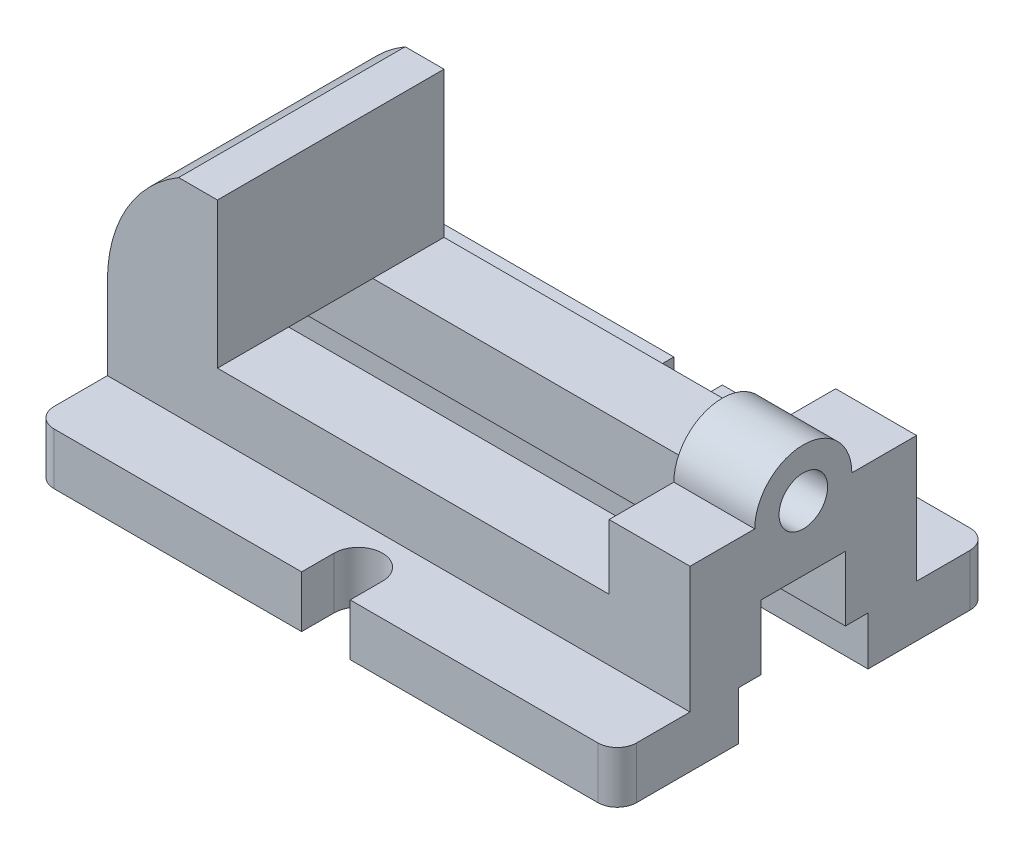
SolidWorks part; units mm, degrees
material "Malleable Cast Iron"
ref_plane "Front Plane" through (0, 0, 0) normal (0, 0, 1) x (1, 0, 0)
ref_plane "Top Plane" through (0, 0, 0) normal (0, 1, 0) x (1, 0, 0)
ref_plane "Right Plane" through (0, 0, 0) normal (1, 0, 0) x (0, 0, -1)
sketch "Sketch1" plane through (0, 0, 0) normal (1, 0, 0) x (0, 0, -1)
  line L0 (0, -17.5) -> (0, 17.5) construction
  line L1 (13, 17.5) -> (35, 17.5)
  line L2 (35, 17.5) -> (35, -1.5)
  line L3 (35, -1.5) -> (57.5, -1.5)
  line L4 (57.5, -1.5) -> (57.5, -17.5)
  line L5 (57.5, -17.5) -> (20, -17.5)
  line L6 (20, -17.5) -> (20, -2.5)
  line L7 (20, -2.5) -> (13, -2.5)
  line L8 (13, -2.5) -> (13, 17.5)
  line L9 (-13, -2.5) -> (-13, 17.5)
  line L10 (-20, -2.5) -> (-13, -2.5)
  line L11 (-20, -17.5) -> (-20, -2.5)
  line L12 (-57.5, -17.5) -> (-20, -17.5)
  line L13 (-57.5, -1.5) -> (-57.5, -17.5)
  line L14 (-35, -1.5) -> (-57.5, -1.5)
  line L15 (-35, 17.5) -> (-35, -1.5)
  line L16 (-13, 17.5) -> (-35, 17.5)
  point P4 (0, 0)
  dimension "D1" = 35
  dimension "D2" = 115
  dimension "D3" = 40
  dimension "D4" = 26
  dimension "D5" = 20
  dimension "D6" = 16
  dimension "D7" = 70
extrude "Boss-Extrude1" add sketch "Sketch1" along normal mid plane 180
sketch "Sketch2" plane through (90, 0, 0) normal (1, 0, 0) x (0, 0, -1)
  line L0 (35, 17.5) -> (-35, 17.5)
  line L1 (-35, 17.5) -> (-35, 37.5)
  line L2 (-35, 37.5) -> (-15, 37.5)
  line L3 (15, 37.5) -> (35, 37.5)
  line L4 (35, 37.5) -> (35, 17.5)
  line L5 (-57.5, -17.5) -> (-20, -17.5) construction
  arc A0 (-15, 37.5) -> (15, 37.5) centre (0, 37.5) cw
  circle A1 centre (0, 37.5) radius 7.5
  dimension "D1" = 15
  dimension "D3" = 15
  dimension "D2" = 55
extrude "Boss-Extrude2" add sketch "Sketch2" against normal blind 25
sketch "Sketch3" plane through (0, 0, -35) normal (0, 0, -1) x (-1, 0, 0)
  line L0 (90, 17.5) -> (56, 17.5)
  line L1 (-65, 17.5) -> (90, 17.5) construction
  line L2 (56, 17.5) -> (56, 62.5)
  line L3 (56, 62.5) -> (68, 62.5)
  line L5 (-90, -17.5) -> (90, -17.5) construction
  line L6 (90, 17.5) -> (90, 23.8218)
  arc A0 (68, 62.5) -> (90, 23.8218) centre (45, 23.8218) cw
  dimension "D3" = 45
  dimension "D1" = 34
  dimension "D2" = 12
  dimension "D4" = 80
extrude "Boss-Extrude3" add sketch "Sketch3" against normal up to surface (70 mm away) up to face at (21.6667, 17.8333, 35)
fillet "Fillet1" radius 6 4 edges at (-90, -9.5, -57.5) (-90, -9.5, 57.5) (90, -9.5, -57.5) (90, -9.5, 57.5)
sketch "Sketch4" plane through (0, 0, 0) normal (0, 1, 0) x (1, 0, 0)
  line L0 (0, -57.5) -> (0, 57.5) construction
  line L1 (84, 57.5) -> (-84, 57.5) construction
  line L2 (0, 67.5) -> (0, 47.5) construction
  line L3 (7.5, 67.5) -> (7.5, 47.5)
  line L4 (-7.5, 67.5) -> (-7.5, 47.5)
  line L5 (0, -67.5) -> (0, -47.5) construction
  line L6 (-7.5, -67.5) -> (-7.5, -47.5)
  line L7 (7.5, -67.5) -> (7.5, -47.5)
  arc A0 (7.5, 67.5) -> (-7.5, 67.5) centre (0, 67.5) ccw
  arc A1 (-7.5, 47.5) -> (7.5, 47.5) centre (0, 47.5) ccw
  arc A2 (-7.5, -67.5) -> (7.5, -67.5) centre (0, -67.5) ccw
  arc A3 (7.5, -47.5) -> (-7.5, -47.5) centre (0, -47.5) ccw
  point P6 (0, 0)
  point P9 (0, 57.5)
  point P15 (0, -57.5)
  dimension "D1" = 7.5
  dimension "D3" = 7.5
  dimension "D2" = 10
  dimension "D4" = 20
extrude "Cut-Extrude1" cut sketch "Sketch4" against normal through all
